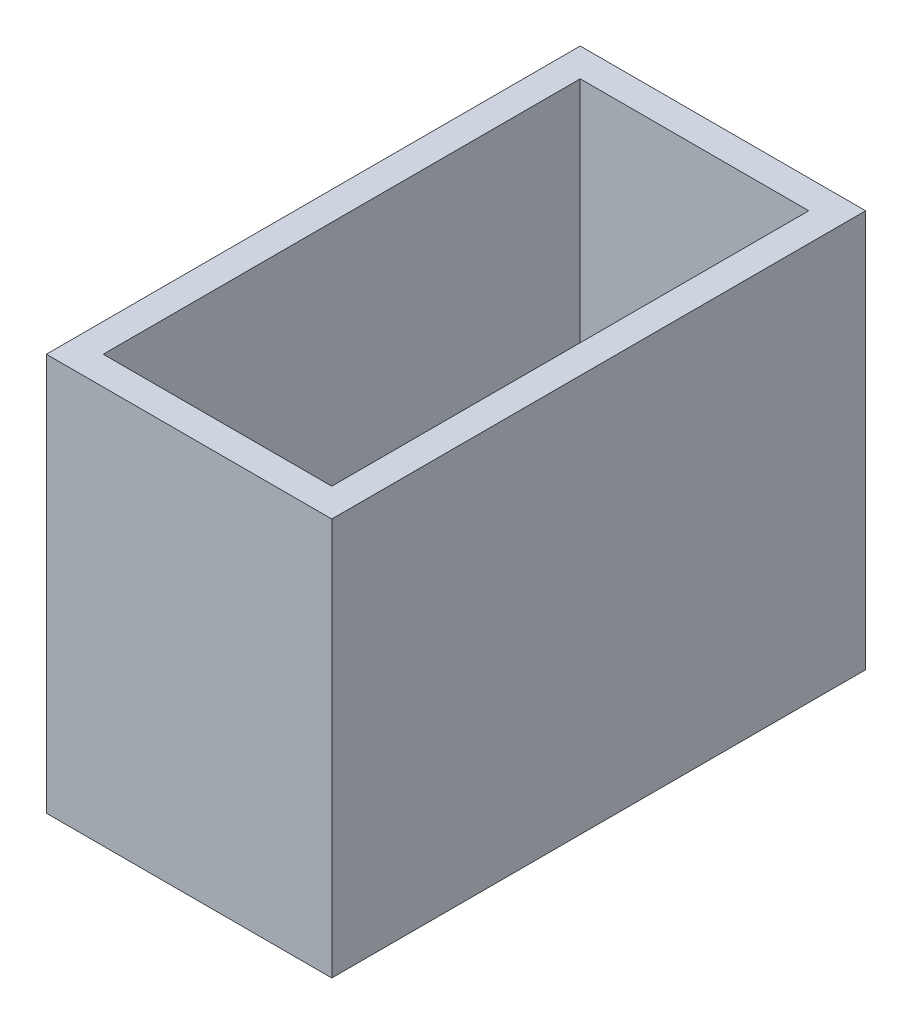
SolidWorks part; units mm, degrees
ref_plane "Front Plane" through (0, 0, 0) normal (0, 0, 1) x (1, 0, 0)
ref_plane "Top Plane" through (0, 0, 0) normal (0, 1, 0) x (1, 0, 0)
ref_plane "Right Plane" through (0, 0, 0) normal (1, 0, 0) x (0, 0, -1)
sketch "Sketch1" plane through (0, 0, 0) normal (0, 1, 0) x (1, 0, 0)
  line L0 (-5.75, 12) -> (-7.18, 12) construction
  line L1 (5.75, 12) -> (-5.75, 12)
  line L2 (5.75, 12) -> (5.75, -12)
  line L3 (5.75, -12) -> (-5.75, -12)
  line L4 (-5.75, 12) -> (-5.75, -12)
  line L5 (0, -12) -> (0, 12) construction
  line L6 (5.75, 0) -> (-5.75, 0) construction
  line L7 (7.18, 13.43) -> (-7.18, 13.43)
  line L8 (7.18, 13.43) -> (7.18, -13.43)
  line L9 (7.18, -13.43) -> (-7.18, -13.43)
  line L10 (-7.18, 13.43) -> (-7.18, -13.43)
  line L11 (0, -13.43) -> (0, 13.43) construction
  line L12 (7.18, 0) -> (-7.18, 0) construction
  line L13 (-5.75, 12) -> (-5.75, 13.43) construction
  point P0 (0, 0)
  point P4 (0, 0)
  dimension "D1" = 1.43
  dimension "D2" = 11.5
  dimension "D3" = 24
extrude "Boss-Extrude1" add sketch "Sketch1" along normal blind 20
